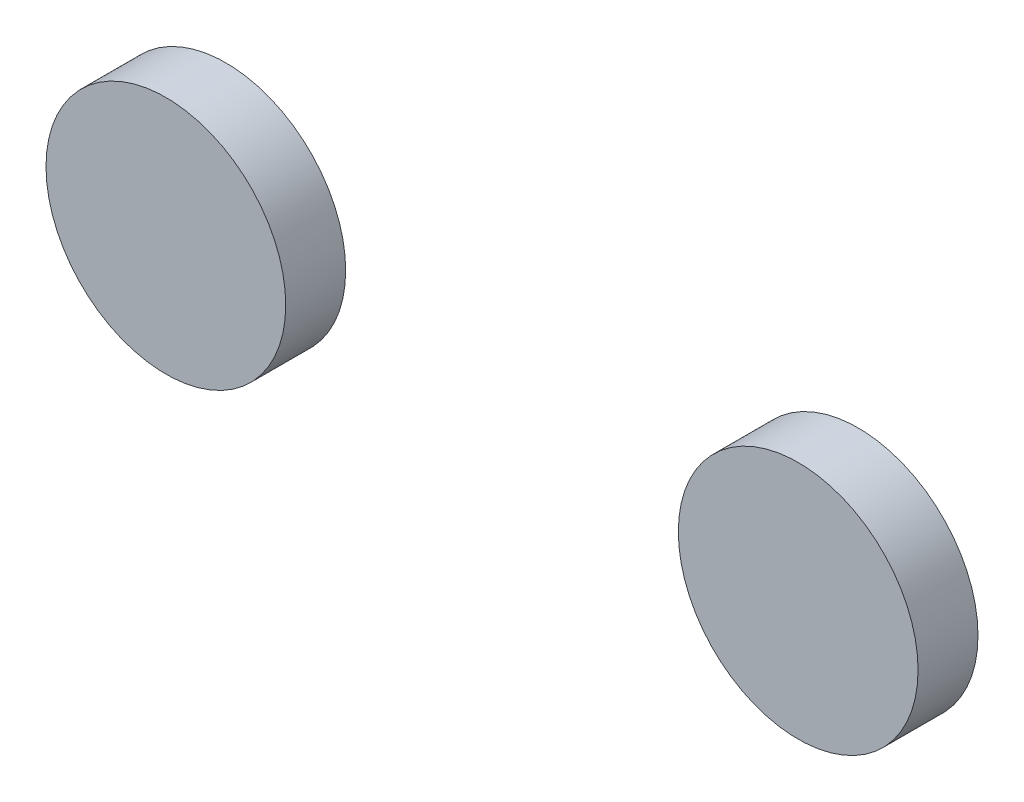
SolidWorks part; units mm, degrees
ref_plane "Front Plane" through (0, 0, 0) normal (0, 0, 1) x (1, 0, 0)
ref_plane "Top Plane" through (0, 0, 0) normal (0, 1, 0) x (1, 0, 0)
ref_plane "Right Plane" through (0, 0, 0) normal (1, 0, 0) x (0, 0, -1)
sketch "Sketch1" plane through (0, 0, 0) normal (0, 0, 1) x (1, 0, 0)
  line L0 (-101.369, 69.9691) -> (98.631, -80.0309)
  line L1 (-101.369, 69.9691) -> (98.631, 69.9691)
  line L2 (-101.369, 69.9691) -> (-101.369, -80.0309)
  line L3 (-101.369, -80.0309) -> (98.631, -80.0309)
  line L4 (98.631, 69.9691) -> (98.631, -80.0309)
  line L5 (-101.369, -80.0309) -> (98.631, 69.9691)
  line L6 (-101.369, -5.0309) -> (98.631, -5.0309)
  circle A3 centre (-51.369, -5.0309) radius 40
  circle A4 centre (54.131, -5.0309) radius 40
  circle A5 centre (-51.369, -5.0309) radius 20
  circle A6 centre (54.131, -5.0309) radius 20
  dimension "D3" = 105.5
  dimension "D1" = 200
  dimension "D2" = 150
extrude "Boss-Extrude1" add sketch "Sketch1" along normal blind 10 contours L6 A5 | L6 A5 | L6 A6 | L6 A6
